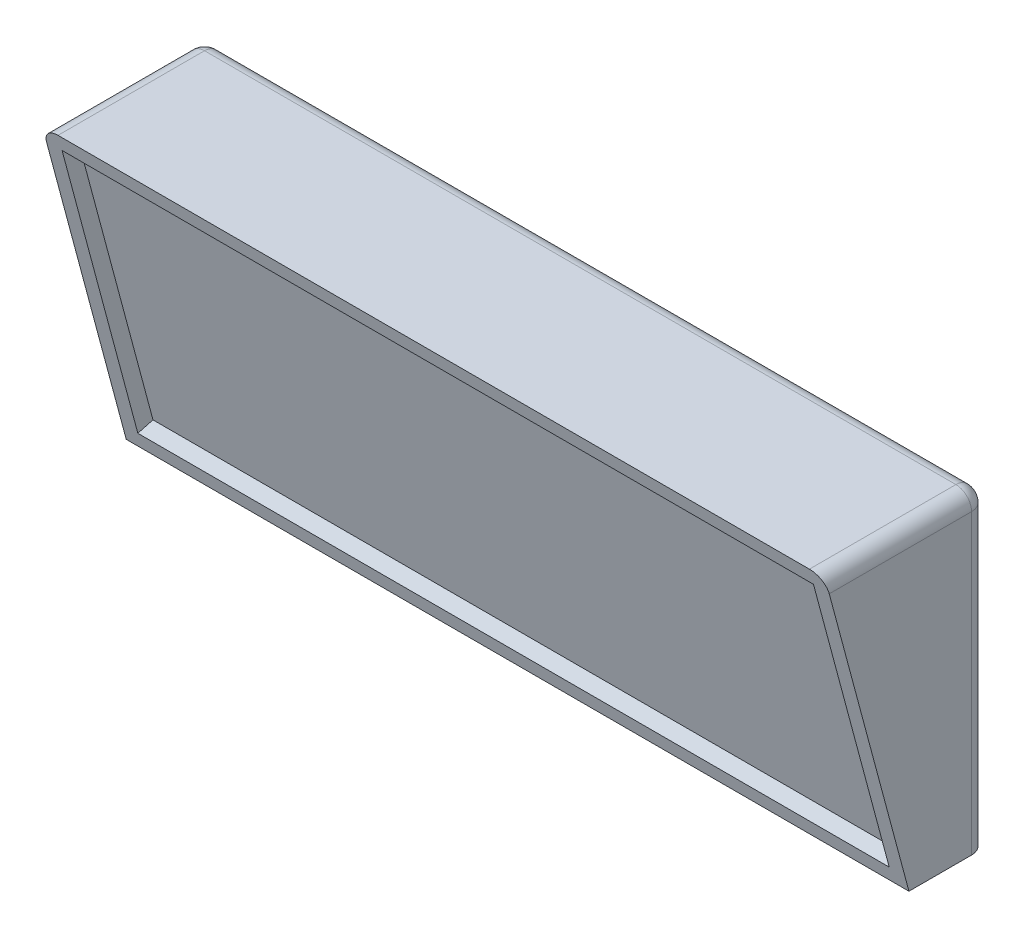
SolidWorks part; units mm, degrees
material "ABS"
ref_plane "Front Plane" through (0, 0, 0) normal (0, 0, 1) x (1, 0, 0)
ref_plane "Top Plane" through (0, 0, 0) normal (0, 1, 0) x (1, 0, 0)
ref_plane "Right Plane" through (0, 0, 0) normal (1, 0, 0) x (0, 0, -1)
sketch "Sketch1" plane through (0, 0, 0) normal (1, 0, 0) x (0, 0, -1)
  line L0 (0, 0) -> (0, 50.8)
  line L1 (0, 50.8) -> (-26.3118, 50.8)
  line L2 (-26.3118, 50.8) -> (-12.7, 0)
  line L3 (-12.7, 0) -> (0, 0)
  point P4 (-31.938, 0)
  dimension "D1" = 50.8
  dimension "D2" = 75
  dimension "D3" = 12.7
extrude "Boss-Extrude1" add sketch "Sketch1" along normal mid plane 127
sketch "Sketch2" plane through (0, -3.175, 11.8493) normal (0, -0.2588, 0.9659) x (1, 0, 0)
  line L8 (-60.96, 53.339) -> (-60.96, 5.827)
  line L9 (-60.96, 5.827) -> (60.96, 5.827)
  line L10 (60.96, 5.827) -> (60.96, 53.339)
  line L11 (60.96, 53.339) -> (-60.96, 53.339)
  line L12 (-60.96, 53.339) -> (-60.96, 5.827)
  line L13 (-60.96, 5.827) -> (60.96, 5.827)
  line L14 (60.96, 5.827) -> (60.96, 53.339)
  line L15 (60.96, 53.339) -> (-60.96, 53.339)
  dimension "D1" = 2.54
extrude "Cut-Extrude1" cut sketch "Sketch2" against normal blind 2.54
fillet "Fillet1" radius 2.54 5 edges at (-63.5, 25.4, 0) (63.5, 25.4, 0) (0, 50.8, 0) (-63.5, 50.8, 13.1559) (63.5, 50.8, 13.1559)
